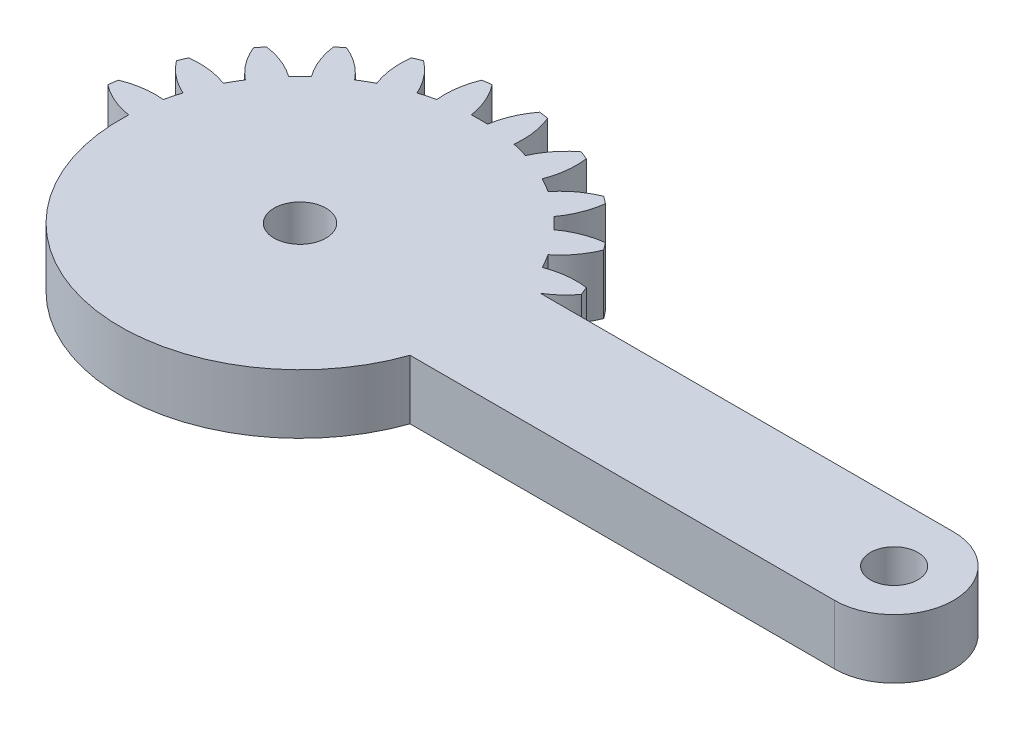
SolidWorks part; units mm, degrees
ref_plane "Front Plane" through (0, 0, 0) normal (0, 0, 1) x (1, 0, 0)
ref_plane "Top Plane" through (0, 0, 0) normal (0, 1, 0) x (1, 0, 0)
ref_plane "Right Plane" through (0, 0, 0) normal (1, 0, 0) x (0, 0, -1)
sketch "Sketch1" plane through (0, 0, 0) normal (0, 1, 0) x (1, 0, 0)
  line L0 (29.8937, 4) -> (2.0816, 4)
  line L1 (2.0816, -4) -> (29.8937, -4)
  line L2 (-10.1063, 12.0928) -> (-10.1063, -12.0927) construction
  arc A0 (2.0816, 4) -> (3.5217, 5.3071) centre (-0.7683, 8.5867) ccw
  arc A1 (3.5217, 5.3071) -> (3.2829, 5.8838) centre (-10.1063, 0) ccw
  arc A2 (3.2829, 5.8838) -> (0.6271, 5.5703) centre (2.5684, 0.5313) ccw
  arc A3 (0.6271, 5.5703) -> (0.0844, 6.5103) centre (-10.1063, 0) ccw
  arc A4 (0.0844, 6.5103) -> (1.6838, 8.6535) centre (-3.3089, 10.711) ccw
  arc A5 (1.6838, 8.6535) -> (1.3038, 9.1487) centre (-10.1063, 0) ccw
  arc A6 (1.3038, 9.1487) -> (-1.1803, 8.1585) centre (1.999, 3.7936) ccw
  arc A7 (-1.1803, 8.1585) -> (-1.9479, 8.926) centre (-10.1063, 0) ccw
  arc A8 (-1.9479, 8.926) -> (-0.9576, 11.4102) centre (-6.3127, 12.1053) ccw
  arc A9 (-0.9576, 11.4102) -> (-1.4528, 11.7901) centre (-10.1063, 0) ccw
  arc A10 (-1.4528, 11.7901) -> (-3.596, 10.1907) centre (0.6046, 6.7975) ccw
  arc A11 (-3.596, 10.1907) -> (-4.5361, 10.7334) centre (-10.1063, 0) ccw
  arc A12 (-4.5361, 10.7334) -> (-4.2225, 13.3892) centre (-9.5751, 12.6747) ccw
  arc A13 (-4.2225, 13.3892) -> (-4.7992, 13.6281) centre (-10.1063, 0) ccw
  arc A14 (-4.7992, 13.6281) -> (-6.4554, 11.5285) centre (-1.5196, 9.3381) ccw
  arc A15 (-6.4554, 11.5285) -> (-7.5039, 11.8094) centre (-10.1063, 0) ccw
  arc A16 (-7.5039, 11.8094) -> (-7.8884, 14.4558) centre (-12.8736, 12.3803) ccw
  arc A17 (-7.8884, 14.4558) -> (-8.5072, 14.5373) centre (-10.1063, 0) ccw
  arc A18 (-8.5072, 14.5373) -> (-9.5636, 12.0806) centre (-4.2291, 11.2423) ccw
  arc A19 (-9.5636, 12.0806) -> (-10.6491, 12.0806) centre (-10.1063, 0) ccw
  arc A20 (-10.6491, 12.0806) -> (-11.7054, 14.5373) centre (-15.9836, 11.2423) ccw
  arc A21 (-11.7054, 14.5373) -> (-12.3243, 14.4558) centre (-10.1063, 0) ccw
  arc A22 (-12.3243, 14.4558) -> (-12.7088, 11.8094) centre (-7.3391, 12.3803) ccw
  arc A23 (-12.7088, 11.8094) -> (-13.7573, 11.5285) centre (-10.1063, 0) ccw
  arc A24 (-13.7573, 11.5285) -> (-15.4135, 13.6281) centre (-18.6931, 9.3381) ccw
  arc A25 (-15.4135, 13.6281) -> (-15.9901, 13.3892) centre (-10.1063, 0) ccw
  arc A26 (-15.9901, 13.3892) -> (-15.6766, 10.7334) centre (-10.6376, 12.6747) ccw
  arc A27 (-15.6766, 10.7334) -> (-16.6166, 10.1907) centre (-10.1063, 0) ccw
  arc A28 (-16.6166, 10.1907) -> (-18.7599, 11.7901) centre (-20.8173, 6.7975) ccw
  arc A29 (-18.7599, 11.7901) -> (-19.255, 11.4102) centre (-10.1063, 0) ccw
  arc A30 (-19.255, 11.4102) -> (-18.2648, 8.926) centre (-13.9, 12.1053) ccw
  arc A31 (-18.2648, 8.926) -> (-19.0324, 8.1585) centre (-10.1063, 0) ccw
  arc A32 (-19.0324, 8.1585) -> (-21.5165, 9.1487) centre (-22.2117, 3.7936) ccw
  arc A33 (-21.5165, 9.1487) -> (-21.8965, 8.6535) centre (-10.1063, 0) ccw
  arc A34 (-21.8965, 8.6535) -> (-20.2971, 6.5103) centre (-16.9038, 10.711) ccw
  arc A35 (-20.2971, 6.5103) -> (-20.8398, 5.5703) centre (-10.1063, 0) ccw
  arc A36 (-20.8398, 5.5703) -> (-23.4956, 5.8838) centre (-22.7811, 0.5313) ccw
  arc A37 (-23.4956, 5.8838) -> (-23.7344, 5.3071) centre (-10.1063, 0) ccw
  arc A38 (-23.7344, 5.3071) -> (-21.6348, 3.6509) centre (-19.4444, 8.5867) ccw
  arc A39 (-21.6348, 3.6509) -> (-21.9157, 2.6025) centre (-10.1063, 0) ccw
  arc A40 (-21.9157, 2.6025) -> (-24.5622, 2.2179) centre (-22.4867, -2.7673) ccw
  arc A41 (-24.5622, 2.2179) -> (-24.6437, 1.5991) centre (-10.1063, 0) ccw
  arc A42 (-24.6437, 1.5991) -> (-22.1869, 0.5427) centre (-21.3486, 5.8773) ccw
  arc A43 (-22.1869, 0.5427) -> (-22.1869, -0.5427) centre (-10.1063, 0) ccw
  arc A44 (-22.1869, -0.5427) -> (-24.6437, -1.5991) centre (-21.3486, -5.8773) ccw
  arc A45 (-24.6437, -1.5991) -> (-24.5622, -2.2179) centre (-10.1063, 0) ccw
  arc A46 (-24.5622, -2.2179) -> (-21.9157, -2.6025) centre (-22.4867, 2.7673) ccw
  arc A47 (-21.9157, -2.6025) -> (-21.6348, -3.6509) centre (-10.1063, 0) ccw
  arc A48 (-21.6348, -3.6509) -> (-23.7344, -5.3071) centre (-19.4444, -8.5867) ccw
  arc A49 (-23.7344, -5.3071) -> (-23.4956, -5.8838) centre (-10.1063, 0) ccw
  arc A50 (-23.4956, -5.8838) -> (-20.8398, -5.5703) centre (-22.7811, -0.5313) ccw
  arc A51 (-20.8398, -5.5703) -> (-20.2971, -6.5103) centre (-10.1063, 0) ccw
  arc A52 (-20.2971, -6.5103) -> (-21.8965, -8.6535) centre (-16.9038, -10.711) ccw
  arc A53 (-21.8965, -8.6535) -> (-21.5165, -9.1487) centre (-10.1063, 0) ccw
  arc A54 (-21.5165, -9.1487) -> (-19.0324, -8.1585) centre (-22.2117, -3.7936) ccw
  arc A55 (-19.0324, -8.1585) -> (-18.2648, -8.926) centre (-10.1063, 0) ccw
  arc A56 (-18.2648, -8.926) -> (-19.255, -11.4102) centre (-13.9, -12.1053) ccw
  arc A57 (-19.255, -11.4102) -> (-18.7599, -11.7901) centre (-10.1063, 0) ccw
  arc A58 (-18.7599, -11.7901) -> (-16.6166, -10.1907) centre (-20.8173, -6.7975) ccw
  arc A59 (-16.6166, -10.1907) -> (-15.6766, -10.7334) centre (-10.1063, 0) ccw
  arc A60 (-15.6766, -10.7334) -> (-15.9901, -13.3892) centre (-10.6376, -12.6747) ccw
  arc A61 (-15.9901, -13.3892) -> (-15.4135, -13.6281) centre (-10.1063, 0) ccw
  arc A62 (-15.4135, -13.6281) -> (-13.7573, -11.5285) centre (-18.6931, -9.3381) ccw
  arc A63 (-13.7573, -11.5285) -> (-12.7088, -11.8094) centre (-10.1063, 0) ccw
  arc A64 (-12.7088, -11.8094) -> (-12.3243, -14.4558) centre (-7.3391, -12.3803) ccw
  arc A65 (-12.3243, -14.4558) -> (-11.7054, -14.5373) centre (-10.1063, 0) ccw
  arc A66 (-11.7054, -14.5373) -> (-10.6491, -12.0806) centre (-15.9836, -11.2423) ccw
  arc A67 (-10.6491, -12.0806) -> (-9.5636, -12.0806) centre (-10.1063, 0) ccw
  arc A68 (-9.5636, -12.0806) -> (-8.5072, -14.5373) centre (-4.2291, -11.2423) ccw
  arc A69 (-8.5072, -14.5373) -> (-7.8884, -14.4558) centre (-10.1063, 0) ccw
  arc A70 (-7.8884, -14.4558) -> (-7.5039, -11.8094) centre (-12.8736, -12.3803) ccw
  arc A71 (-7.5039, -11.8094) -> (-6.4554, -11.5285) centre (-10.1063, 0) ccw
  arc A72 (-6.4554, -11.5285) -> (-4.7992, -13.6281) centre (-1.5196, -9.3381) ccw
  arc A73 (-4.7992, -13.6281) -> (-4.2225, -13.3892) centre (-10.1063, 0) ccw
  arc A74 (-4.2225, -13.3892) -> (-4.5361, -10.7334) centre (-9.5751, -12.6747) ccw
  arc A75 (-4.5361, -10.7334) -> (-3.596, -10.1907) centre (-10.1063, 0) ccw
  arc A76 (-3.596, -10.1907) -> (-1.4528, -11.7901) centre (0.6046, -6.7975) ccw
  arc A77 (-1.4528, -11.7901) -> (-0.9576, -11.4102) centre (-10.1063, 0) ccw
  arc A78 (-0.9576, -11.4102) -> (-1.9479, -8.926) centre (-6.3127, -12.1053) ccw
  arc A79 (-1.9479, -8.926) -> (-1.1803, -8.1585) centre (-10.1063, 0) ccw
  arc A80 (-1.1803, -8.1585) -> (1.3038, -9.1487) centre (1.999, -3.7936) ccw
  arc A81 (1.3038, -9.1487) -> (1.6838, -8.6535) centre (-10.1063, 0) ccw
  arc A82 (1.6838, -8.6535) -> (0.0844, -6.5103) centre (-3.3089, -10.711) ccw
  arc A83 (0.0844, -6.5103) -> (0.6271, -5.5703) centre (-10.1063, 0) ccw
  arc A84 (0.6271, -5.5703) -> (3.2829, -5.8838) centre (2.5684, -0.5313) ccw
  arc A85 (3.2829, -5.8838) -> (3.5217, -5.3071) centre (-10.1063, 0) ccw
  arc A86 (3.5217, -5.3071) -> (2.0816, -4) centre (-0.7683, -8.5867) ccw
  arc A87 (29.8937, -4) -> (29.8937, 4) centre (29.8937, 0) ccw
  circle A88 centre (-10.1063, 0) radius 1.75
  circle A89 centre (29.8937, 0) radius 1.6
  dimension "D1" = 3.5
  dimension "D2" = 3.2
  dimension "D3" = 40
  dimension "D4" = 4
  dimension "D5" = 24.1855
extrude "Boss-Extrude1" add sketch "Sketch1" along normal blind 4
sketch "Sketch2" plane through (0, 4, 0) normal (0, 1, 0) x (1, 0, 0)
  line L0 (2.0816, -4) -> (1.3057, -4)
  line L2 (29.8937, 4) -> (2.0816, 4)
  line L3 (2.0816, -4) -> (29.8937, -4)
  line L4 (29.8937, 4) -> (2.0816, 4)
  line L5 (2.0816, -4) -> (29.8937, -4)
  circle A0 centre (-10.1063, 0) radius 12.0927
  arc A88 (29.8937, -4) -> (29.8937, 4) centre (29.8937, 0) ccw
  arc A89 (2.0816, 4) -> (3.5217, 5.3071) centre (-0.7683, 8.5867) ccw
  arc A90 (3.5217, 5.3071) -> (3.2829, 5.8838) centre (-10.1063, 0) ccw
  arc A91 (3.2829, 5.8838) -> (0.6271, 5.5703) centre (2.5684, 0.5313) ccw
  arc A92 (0.6271, 5.5703) -> (0.0844, 6.5103) centre (-10.1063, 0) ccw
  arc A93 (0.0844, 6.5103) -> (1.6838, 8.6535) centre (-3.3089, 10.711) ccw
  arc A94 (1.6838, 8.6535) -> (1.3038, 9.1487) centre (-10.1063, 0) ccw
  arc A95 (1.3038, 9.1487) -> (-1.1803, 8.1585) centre (1.999, 3.7936) ccw
  arc A96 (-1.1803, 8.1585) -> (-1.9479, 8.926) centre (-10.1063, 0) ccw
  arc A97 (-1.9479, 8.926) -> (-0.9576, 11.4102) centre (-6.3127, 12.1053) ccw
  arc A98 (-0.9576, 11.4102) -> (-1.4528, 11.7901) centre (-10.1063, 0) ccw
  arc A99 (-1.4528, 11.7901) -> (-3.596, 10.1907) centre (0.6046, 6.7975) ccw
  arc A100 (-3.596, 10.1907) -> (-4.5361, 10.7334) centre (-10.1063, 0) ccw
  arc A101 (-4.5361, 10.7334) -> (-4.2225, 13.3892) centre (-9.5751, 12.6747) ccw
  arc A102 (-4.2225, 13.3892) -> (-4.7992, 13.6281) centre (-10.1063, 0) ccw
  arc A103 (-4.7992, 13.6281) -> (-6.4554, 11.5285) centre (-1.5196, 9.3381) ccw
  arc A104 (-6.4554, 11.5285) -> (-7.5039, 11.8094) centre (-10.1063, 0) ccw
  arc A105 (-7.5039, 11.8094) -> (-7.8884, 14.4558) centre (-12.8736, 12.3803) ccw
  arc A106 (-7.8884, 14.4558) -> (-8.5072, 14.5373) centre (-10.1063, 0) ccw
  arc A107 (-8.5072, 14.5373) -> (-9.5636, 12.0806) centre (-4.2291, 11.2423) ccw
  arc A108 (-9.5636, 12.0806) -> (-10.6491, 12.0806) centre (-10.1063, 0) ccw
  arc A109 (-10.6491, 12.0806) -> (-11.7054, 14.5373) centre (-15.9836, 11.2423) ccw
  arc A110 (-11.7054, 14.5373) -> (-12.3243, 14.4558) centre (-10.1063, 0) ccw
  arc A111 (-12.3243, 14.4558) -> (-12.7088, 11.8094) centre (-7.3391, 12.3803) ccw
  arc A112 (-12.7088, 11.8094) -> (-13.7573, 11.5285) centre (-10.1063, 0) ccw
  arc A113 (-13.7573, 11.5285) -> (-15.4135, 13.6281) centre (-18.6931, 9.3381) ccw
  arc A114 (-15.4135, 13.6281) -> (-15.9901, 13.3892) centre (-10.1063, 0) ccw
  arc A115 (-15.9901, 13.3892) -> (-15.6766, 10.7334) centre (-10.6376, 12.6747) ccw
  arc A116 (-15.6766, 10.7334) -> (-16.6166, 10.1907) centre (-10.1063, 0) ccw
  arc A117 (-16.6166, 10.1907) -> (-18.7599, 11.7901) centre (-20.8173, 6.7975) ccw
  arc A118 (-18.7599, 11.7901) -> (-19.255, 11.4102) centre (-10.1063, 0) ccw
  arc A119 (-19.255, 11.4102) -> (-18.2648, 8.926) centre (-13.9, 12.1053) ccw
  arc A120 (-18.2648, 8.926) -> (-19.0324, 8.1585) centre (-10.1063, 0) ccw
  arc A121 (-19.0324, 8.1585) -> (-21.5165, 9.1487) centre (-22.2117, 3.7936) ccw
  arc A122 (-21.5165, 9.1487) -> (-21.8965, 8.6535) centre (-10.1063, 0) ccw
  arc A123 (-21.8965, 8.6535) -> (-20.2971, 6.5103) centre (-16.9038, 10.711) ccw
  arc A124 (-20.2971, 6.5103) -> (-20.8398, 5.5703) centre (-10.1063, 0) ccw
  arc A125 (-20.8398, 5.5703) -> (-23.4956, 5.8838) centre (-22.7811, 0.5313) ccw
  arc A126 (-23.4956, 5.8838) -> (-23.7344, 5.3071) centre (-10.1063, 0) ccw
  arc A127 (-23.7344, 5.3071) -> (-21.6348, 3.6509) centre (-19.4444, 8.5867) ccw
  arc A128 (-21.6348, 3.6509) -> (-21.9157, 2.6025) centre (-10.1063, 0) ccw
  arc A129 (-21.9157, 2.6025) -> (-24.5622, 2.2179) centre (-22.4867, -2.7673) ccw
  arc A130 (-24.5622, 2.2179) -> (-24.6437, 1.5991) centre (-10.1063, 0) ccw
  arc A131 (-24.6437, 1.5991) -> (-22.1869, 0.5427) centre (-21.3486, 5.8773) ccw
  arc A132 (-22.1869, 0.5427) -> (-22.1869, -0.5427) centre (-10.1063, 0) ccw
  arc A133 (-22.1869, -0.5427) -> (-24.6437, -1.5991) centre (-21.3486, -5.8773) ccw
  arc A134 (-24.6437, -1.5991) -> (-24.5622, -2.2179) centre (-10.1063, 0) ccw
  arc A135 (-24.5622, -2.2179) -> (-21.9157, -2.6025) centre (-22.4867, 2.7673) ccw
  arc A136 (-21.9157, -2.6025) -> (-21.6348, -3.6509) centre (-10.1063, 0) ccw
  arc A137 (-21.6348, -3.6509) -> (-23.7344, -5.3071) centre (-19.4444, -8.5867) ccw
  arc A138 (-23.7344, -5.3071) -> (-23.4956, -5.8838) centre (-10.1063, 0) ccw
  arc A139 (-23.4956, -5.8838) -> (-20.8398, -5.5703) centre (-22.7811, -0.5313) ccw
  arc A140 (-20.8398, -5.5703) -> (-20.2971, -6.5103) centre (-10.1063, 0) ccw
  arc A141 (-20.2971, -6.5103) -> (-21.8965, -8.6535) centre (-16.9038, -10.711) ccw
  arc A142 (-21.8965, -8.6535) -> (-21.5165, -9.1487) centre (-10.1063, 0) ccw
  arc A143 (-21.5165, -9.1487) -> (-19.0324, -8.1585) centre (-22.2117, -3.7936) ccw
  arc A144 (-19.0324, -8.1585) -> (-18.2648, -8.926) centre (-10.1063, 0) ccw
  arc A145 (-18.2648, -8.926) -> (-19.255, -11.4102) centre (-13.9, -12.1053) ccw
  arc A146 (-19.255, -11.4102) -> (-18.7599, -11.7901) centre (-10.1063, 0) ccw
  arc A147 (-18.7599, -11.7901) -> (-16.6166, -10.1907) centre (-20.8173, -6.7975) ccw
  arc A148 (-16.6166, -10.1907) -> (-15.6766, -10.7334) centre (-10.1063, 0) ccw
  arc A149 (-15.6766, -10.7334) -> (-15.9901, -13.3892) centre (-10.6376, -12.6747) ccw
  arc A150 (-15.9901, -13.3892) -> (-15.4135, -13.6281) centre (-10.1063, 0) ccw
  arc A151 (-15.4135, -13.6281) -> (-13.7573, -11.5285) centre (-18.6931, -9.3381) ccw
  arc A152 (-13.7573, -11.5285) -> (-12.7088, -11.8094) centre (-10.1063, 0) ccw
  arc A153 (-12.7088, -11.8094) -> (-12.3243, -14.4558) centre (-7.3391, -12.3803) ccw
  arc A154 (-12.3243, -14.4558) -> (-11.7054, -14.5373) centre (-10.1063, 0) ccw
  arc A155 (-11.7054, -14.5373) -> (-10.6491, -12.0806) centre (-15.9836, -11.2423) ccw
  arc A156 (-10.6491, -12.0806) -> (-9.5636, -12.0806) centre (-10.1063, 0) ccw
  arc A157 (-9.5636, -12.0806) -> (-8.5072, -14.5373) centre (-4.2291, -11.2423) ccw
  arc A158 (-8.5072, -14.5373) -> (-7.8884, -14.4558) centre (-10.1063, 0) ccw
  arc A159 (-7.8884, -14.4558) -> (-7.5039, -11.8094) centre (-12.8736, -12.3803) ccw
  arc A160 (-7.5039, -11.8094) -> (-6.4554, -11.5285) centre (-10.1063, 0) ccw
  arc A161 (-6.4554, -11.5285) -> (-4.7992, -13.6281) centre (-1.5196, -9.3381) ccw
  arc A162 (-4.7992, -13.6281) -> (-4.2225, -13.3892) centre (-10.1063, 0) ccw
  arc A163 (-4.2225, -13.3892) -> (-4.5361, -10.7334) centre (-9.5751, -12.6747) ccw
  arc A164 (-4.5361, -10.7334) -> (-3.596, -10.1907) centre (-10.1063, 0) ccw
  arc A165 (-3.596, -10.1907) -> (-1.4528, -11.7901) centre (0.6046, -6.7975) ccw
  arc A166 (-1.4528, -11.7901) -> (-0.9576, -11.4102) centre (-10.1063, 0) ccw
  arc A167 (-0.9576, -11.4102) -> (-1.9479, -8.926) centre (-6.3127, -12.1053) ccw
  arc A168 (-1.9479, -8.926) -> (-1.1803, -8.1585) centre (-10.1063, 0) ccw
  arc A169 (-1.1803, -8.1585) -> (1.3038, -9.1487) centre (1.999, -3.7936) ccw
  arc A170 (1.3038, -9.1487) -> (1.6838, -8.6535) centre (-10.1063, 0) ccw
  arc A171 (1.6838, -8.6535) -> (0.0844, -6.5103) centre (-3.3089, -10.711) ccw
  arc A172 (0.0844, -6.5103) -> (0.6271, -5.5703) centre (-10.1063, 0) ccw
  arc A173 (0.6271, -5.5703) -> (3.2829, -5.8838) centre (2.5684, -0.5313) ccw
  arc A174 (3.2829, -5.8838) -> (3.5217, -5.3071) centre (-10.1063, 0) ccw
  arc A175 (3.5217, -5.3071) -> (2.0816, -4) centre (-0.7683, -8.5867) ccw
  arc A176 (29.8937, -4) -> (29.8937, 4) centre (29.8937, 0) ccw
  arc A177 (2.0816, 4) -> (3.5217, 5.3071) centre (-0.7683, 8.5867) ccw
  arc A178 (3.5217, 5.3071) -> (3.2829, 5.8838) centre (-10.1063, 0) ccw
  arc A179 (3.2829, 5.8838) -> (0.6271, 5.5703) centre (2.5684, 0.5313) ccw
  arc A180 (0.6271, 5.5703) -> (0.0844, 6.5103) centre (-10.1063, 0) ccw
  arc A181 (0.0844, 6.5103) -> (1.6838, 8.6535) centre (-3.3089, 10.711) ccw
  arc A182 (1.6838, 8.6535) -> (1.3038, 9.1487) centre (-10.1063, 0) ccw
  arc A183 (1.3038, 9.1487) -> (-1.1803, 8.1585) centre (1.999, 3.7936) ccw
  arc A184 (-1.1803, 8.1585) -> (-1.9479, 8.926) centre (-10.1063, 0) ccw
  arc A185 (-1.9479, 8.926) -> (-0.9576, 11.4102) centre (-6.3127, 12.1053) ccw
  arc A186 (-0.9576, 11.4102) -> (-1.4528, 11.7901) centre (-10.1063, 0) ccw
  arc A187 (-1.4528, 11.7901) -> (-3.596, 10.1907) centre (0.6046, 6.7975) ccw
  arc A188 (-3.596, 10.1907) -> (-4.5361, 10.7334) centre (-10.1063, 0) ccw
  arc A189 (-4.5361, 10.7334) -> (-4.2225, 13.3892) centre (-9.5751, 12.6747) ccw
  arc A190 (-4.2225, 13.3892) -> (-4.7992, 13.6281) centre (-10.1063, 0) ccw
  arc A191 (-4.7992, 13.6281) -> (-6.4554, 11.5285) centre (-1.5196, 9.3381) ccw
  arc A192 (-6.4554, 11.5285) -> (-7.5039, 11.8094) centre (-10.1063, 0) ccw
  arc A193 (-7.5039, 11.8094) -> (-7.8884, 14.4558) centre (-12.8736, 12.3803) ccw
  arc A194 (-7.8884, 14.4558) -> (-8.5072, 14.5373) centre (-10.1063, 0) ccw
  arc A195 (-8.5072, 14.5373) -> (-9.5636, 12.0806) centre (-4.2291, 11.2423) ccw
  arc A196 (-9.5636, 12.0806) -> (-10.6491, 12.0806) centre (-10.1063, 0) ccw
  arc A197 (-10.6491, 12.0806) -> (-11.7054, 14.5373) centre (-15.9836, 11.2423) ccw
  arc A198 (-11.7054, 14.5373) -> (-12.3243, 14.4558) centre (-10.1063, 0) ccw
  arc A199 (-12.3243, 14.4558) -> (-12.7088, 11.8094) centre (-7.3391, 12.3803) ccw
  arc A200 (-12.7088, 11.8094) -> (-13.7573, 11.5285) centre (-10.1063, 0) ccw
  arc A201 (-13.7573, 11.5285) -> (-15.4135, 13.6281) centre (-18.6931, 9.3381) ccw
  arc A202 (-15.4135, 13.6281) -> (-15.9901, 13.3892) centre (-10.1063, 0) ccw
  arc A203 (-15.9901, 13.3892) -> (-15.6766, 10.7334) centre (-10.6376, 12.6747) ccw
  arc A204 (-15.6766, 10.7334) -> (-16.6166, 10.1907) centre (-10.1063, 0) ccw
  arc A205 (-16.6166, 10.1907) -> (-18.7599, 11.7901) centre (-20.8173, 6.7975) ccw
  arc A206 (-18.7599, 11.7901) -> (-19.255, 11.4102) centre (-10.1063, 0) ccw
  arc A207 (-19.255, 11.4102) -> (-18.2648, 8.926) centre (-13.9, 12.1053) ccw
  arc A208 (-18.2648, 8.926) -> (-19.0324, 8.1585) centre (-10.1063, 0) ccw
  arc A209 (-19.0324, 8.1585) -> (-21.5165, 9.1487) centre (-22.2117, 3.7936) ccw
  arc A210 (-21.5165, 9.1487) -> (-21.8965, 8.6535) centre (-10.1063, 0) ccw
  arc A211 (-21.8965, 8.6535) -> (-20.2971, 6.5103) centre (-16.9038, 10.711) ccw
  arc A212 (-20.2971, 6.5103) -> (-20.8398, 5.5703) centre (-10.1063, 0) ccw
  arc A213 (-20.8398, 5.5703) -> (-23.4956, 5.8838) centre (-22.7811, 0.5313) ccw
  arc A214 (-23.4956, 5.8838) -> (-23.7344, 5.3071) centre (-10.1063, 0) ccw
  arc A215 (-23.7344, 5.3071) -> (-21.6348, 3.6509) centre (-19.4444, 8.5867) ccw
  arc A216 (-21.6348, 3.6509) -> (-21.9157, 2.6025) centre (-10.1063, 0) ccw
  arc A217 (-21.9157, 2.6025) -> (-24.5622, 2.2179) centre (-22.4867, -2.7673) ccw
  arc A218 (-24.5622, 2.2179) -> (-24.6437, 1.5991) centre (-10.1063, 0) ccw
  arc A219 (-24.6437, 1.5991) -> (-22.1869, 0.5427) centre (-21.3486, 5.8773) ccw
  arc A220 (-22.1869, 0.5427) -> (-22.1869, -0.5427) centre (-10.1063, 0) ccw
  arc A221 (-22.1869, -0.5427) -> (-24.6437, -1.5991) centre (-21.3486, -5.8773) ccw
  arc A222 (-24.6437, -1.5991) -> (-24.5622, -2.2179) centre (-10.1063, 0) ccw
  arc A223 (-24.5622, -2.2179) -> (-21.9157, -2.6025) centre (-22.4867, 2.7673) ccw
  arc A224 (-21.9157, -2.6025) -> (-21.6348, -3.6509) centre (-10.1063, 0) ccw
  arc A225 (-21.6348, -3.6509) -> (-23.7344, -5.3071) centre (-19.4444, -8.5867) ccw
  arc A226 (-23.7344, -5.3071) -> (-23.4956, -5.8838) centre (-10.1063, 0) ccw
  arc A227 (-23.4956, -5.8838) -> (-20.8398, -5.5703) centre (-22.7811, -0.5313) ccw
  arc A228 (-20.8398, -5.5703) -> (-20.2971, -6.5103) centre (-10.1063, 0) ccw
  arc A229 (-20.2971, -6.5103) -> (-21.8965, -8.6535) centre (-16.9038, -10.711) ccw
  arc A230 (-21.8965, -8.6535) -> (-21.5165, -9.1487) centre (-10.1063, 0) ccw
  arc A231 (-21.5165, -9.1487) -> (-19.0324, -8.1585) centre (-22.2117, -3.7936) ccw
  arc A232 (-19.0324, -8.1585) -> (-18.2648, -8.926) centre (-10.1063, 0) ccw
  arc A233 (-18.2648, -8.926) -> (-19.255, -11.4102) centre (-13.9, -12.1053) ccw
  arc A234 (-19.255, -11.4102) -> (-18.7599, -11.7901) centre (-10.1063, 0) ccw
  arc A235 (-18.7599, -11.7901) -> (-16.6166, -10.1907) centre (-20.8173, -6.7975) ccw
  arc A236 (-16.6166, -10.1907) -> (-15.6766, -10.7334) centre (-10.1063, 0) ccw
  arc A237 (-15.6766, -10.7334) -> (-15.9901, -13.3892) centre (-10.6376, -12.6747) ccw
  arc A238 (-15.9901, -13.3892) -> (-15.4135, -13.6281) centre (-10.1063, 0) ccw
  arc A239 (-15.4135, -13.6281) -> (-13.7573, -11.5285) centre (-18.6931, -9.3381) ccw
  arc A240 (-13.7573, -11.5285) -> (-12.7088, -11.8094) centre (-10.1063, 0) ccw
  arc A241 (-12.7088, -11.8094) -> (-12.3243, -14.4558) centre (-7.3391, -12.3803) ccw
  arc A242 (-12.3243, -14.4558) -> (-11.7054, -14.5373) centre (-10.1063, 0) ccw
  arc A243 (-11.7054, -14.5373) -> (-10.6491, -12.0806) centre (-15.9836, -11.2423) ccw
  arc A244 (-10.6491, -12.0806) -> (-9.5636, -12.0806) centre (-10.1063, 0) ccw
  arc A245 (-9.5636, -12.0806) -> (-8.5072, -14.5373) centre (-4.2291, -11.2423) ccw
  arc A246 (-8.5072, -14.5373) -> (-7.8884, -14.4558) centre (-10.1063, 0) ccw
  arc A247 (-7.8884, -14.4558) -> (-7.5039, -11.8094) centre (-12.8736, -12.3803) ccw
  arc A248 (-7.5039, -11.8094) -> (-6.4554, -11.5285) centre (-10.1063, 0) ccw
  arc A249 (-6.4554, -11.5285) -> (-4.7992, -13.6281) centre (-1.5196, -9.3381) ccw
  arc A250 (-4.7992, -13.6281) -> (-4.2225, -13.3892) centre (-10.1063, 0) ccw
  arc A251 (-4.2225, -13.3892) -> (-4.5361, -10.7334) centre (-9.5751, -12.6747) ccw
  arc A252 (-4.5361, -10.7334) -> (-3.596, -10.1907) centre (-10.1063, 0) ccw
  arc A253 (-3.596, -10.1907) -> (-1.4528, -11.7901) centre (0.6046, -6.7975) ccw
  arc A254 (-1.4528, -11.7901) -> (-0.9576, -11.4102) centre (-10.1063, 0) ccw
  arc A255 (-0.9576, -11.4102) -> (-1.9479, -8.926) centre (-6.3127, -12.1053) ccw
  arc A256 (-1.9479, -8.926) -> (-1.1803, -8.1585) centre (-10.1063, 0) ccw
  arc A257 (-1.1803, -8.1585) -> (1.3038, -9.1487) centre (1.999, -3.7936) ccw
  arc A258 (1.3038, -9.1487) -> (1.6838, -8.6535) centre (-10.1063, 0) ccw
  arc A259 (1.6838, -8.6535) -> (0.0844, -6.5103) centre (-3.3089, -10.711) ccw
  arc A260 (0.0844, -6.5103) -> (0.6271, -5.5703) centre (-10.1063, 0) ccw
  arc A261 (0.6271, -5.5703) -> (3.2829, -5.8838) centre (2.5684, -0.5313) ccw
  arc A262 (3.2829, -5.8838) -> (3.5217, -5.3071) centre (-10.1063, 0) ccw
  arc A263 (3.5217, -5.3071) -> (2.0816, -4) centre (-0.7683, -8.5867) ccw
  dimension "D1" = 0
extrude "Cut-Extrude1" cut sketch "Sketch2" against normal blind 10 contours A222 A223 A0 A221 | A226 A227 A0 A225 | A230 A231 A0 A229 | A234 A235 A0 A233 | A238 A239 A0 A237 | A242 A243 A0 A241 | A246 A247 A0 A245 | A250 A251 A0 A249 | A254 A255 A0 A253 | A258 A259 A0 A257 | A262 A263 L0 A0 A261
